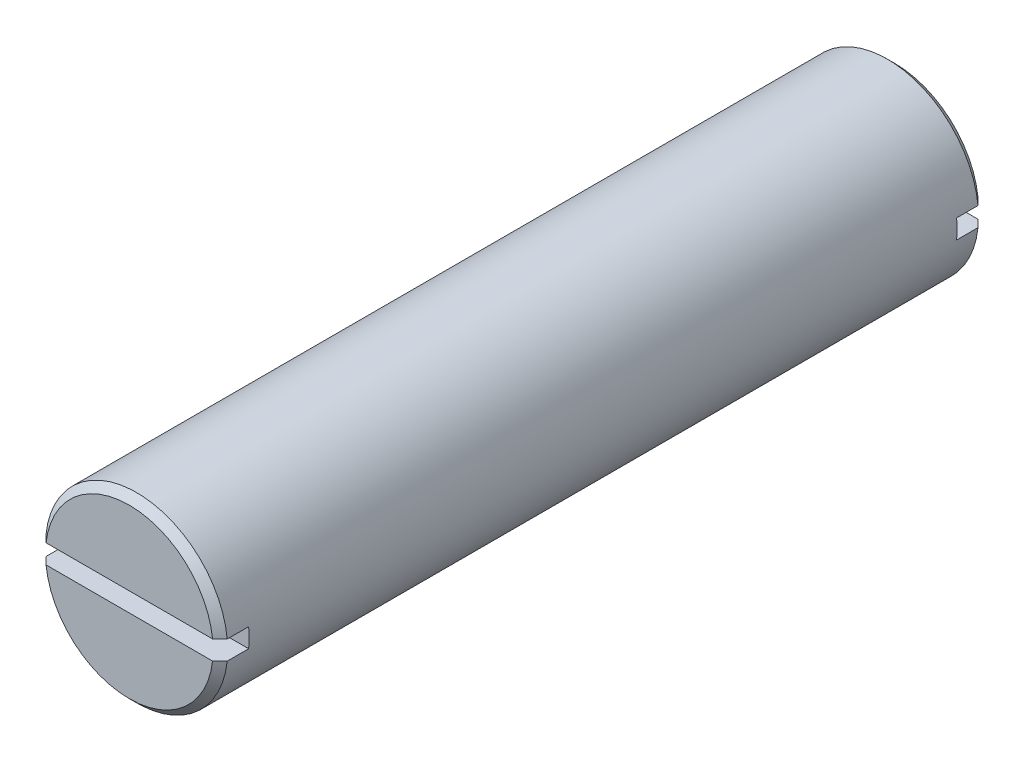
SolidWorks part; units mm, degrees
material "316 SSTL"
ref_plane "Front" through (0, 0, 0) normal (0, 0, 1) x (1, 0, 0)
ref_plane "Top" through (0, 0, 0) normal (0, 1, 0) x (1, 0, 0)
ref_plane "Right" through (0, 0, 0) normal (1, 0, 0) x (0, 0, -1)
sketch "Sketch1" plane through (0, 0, 0) normal (0, 0, 1) x (1, 0, 0)
  circle A0 centre (0, 0) radius 9.525
  dimension "D1" = 19.05
extrude "Boss-Extrude1" add sketch "Sketch1" along normal mid plane 80
cosmetic thread "Cosmetic Thread1" parameters "D2"=16.256
chamfer "Chamfer1" distance 0.762 angle 45 2 edges at (9.525, 0, -40) (9.525, 0, 40)
sketch "Sketch2" plane through (0, 0, 0) normal (1, 0, 0) x (0, 0, -1)
  line L0 (0, 0) -> (-37, 0) construction
  line L1 (-40, 1) -> (-37, 1)
  line L2 (-40, 1) -> (-40, -1)
  line L3 (-40, -1) -> (-37, -1)
  line L4 (-37, 1) -> (-37, -1)
  line L5 (37, 1) -> (40, 1)
  line L6 (37, 1) -> (37, -1)
  line L7 (37, -1) -> (40, -1)
  line L8 (40, 1) -> (40, -1)
  line L9 (0, 0) -> (37, 0) construction
  line L10 (-40, 8.763) -> (-40, -8.763) construction
  line L11 (40, -8.763) -> (40, 8.763) construction
  dimension "D1" = 2
  dimension "D2" = 2
  dimension "D3" = 3
  dimension "D4" = 3
extrude "Cut-Extrude1" cut sketch "Sketch2" against normal through all and the other way through all
